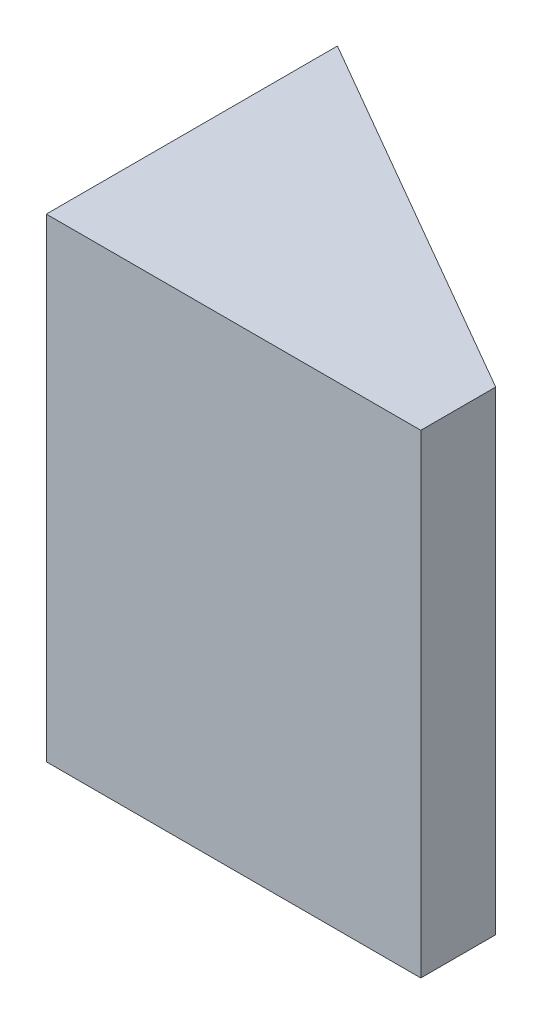
SolidWorks part; units mm, degrees
ref_plane "Ebene vorne" through (0, 0, 0) normal (0, 0, 1) x (1, 0, 0)
ref_plane "Ebene oben" through (0, 0, 0) normal (0, 1, 0) x (1, 0, 0)
ref_plane "Ebene rechts" through (0, 0, 0) normal (1, 0, 0) x (0, 0, -1)
sketch "Skizze1" plane through (0, 0, 0) normal (0, 0, 1) x (1, 0, 0)
  line L1 (-7.5, -9.5) -> (7.5, -9.5)
  line L2 (-7.5, -9.5) -> (-7.5, 9.5)
  line L3 (-7.5, 9.5) -> (7.5, 9.5)
  line L4 (7.5, -9.5) -> (7.5, 9.5)
  line L5 (-7.5, -9.5) -> (7.5, 9.5) construction
  line L6 (-7.5, 9.5) -> (7.5, -9.5) construction
  point P0 (0, 0)
  dimension "D1" = 15
  dimension "D2" = 19
extrude "Aufsatz-Linear austragen1" add sketch "Skizze1" along normal blind 3
sketch "Skizze3" plane through (0, 9.5, 0) normal (0, 1, 0) x (1, 0, 0)
  line L0 (-7.5, 0) -> (-7.5, 8.6603)
  line L1 (-7.5, 8.6603) -> (7.5, 0)
  line L2 (7.5, 0) -> (-7.5, 0) construction
  line L3 (-7.5, 0) -> (7.5, 0)
  dimension "D1" = 30
extrude "Aufsatz-Linear austragen2" add sketch "Skizze3" against normal blind 19
